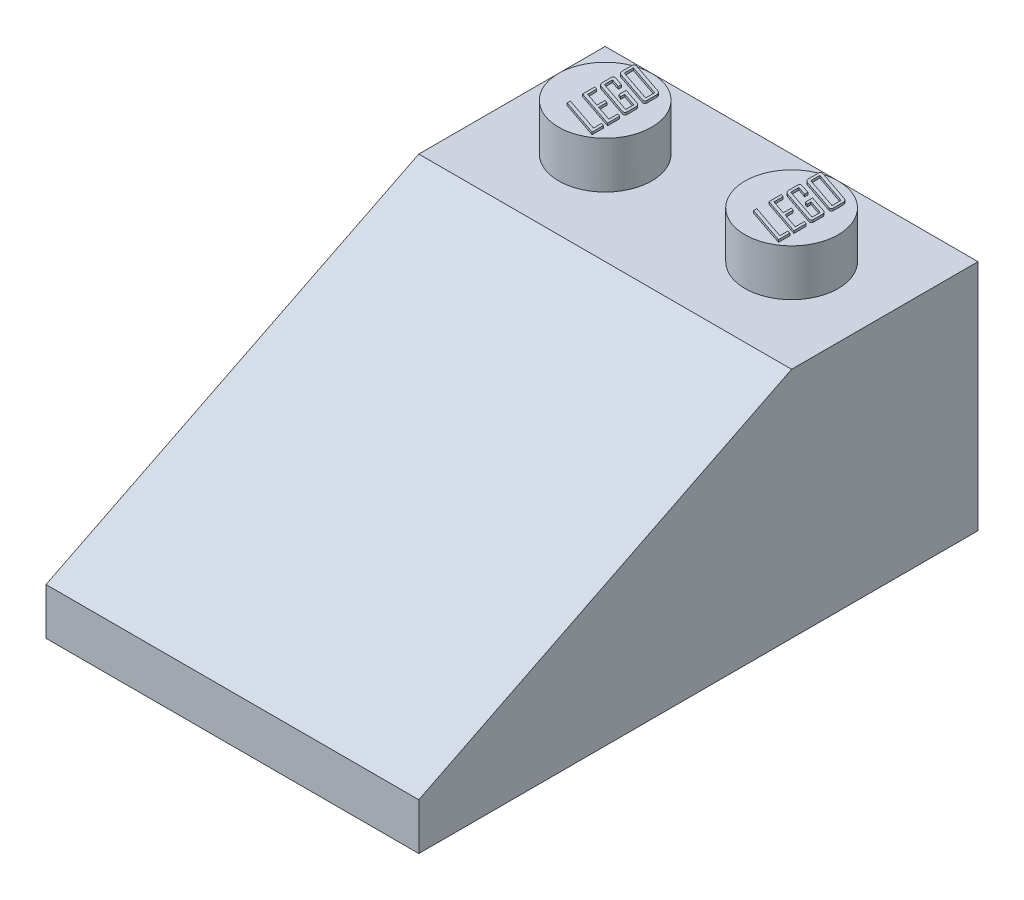
SolidWorks part; units mm, degrees
material "ABS"
ref_plane "Front Plane" through (0, 0, 0) normal (0, 0, 1) x (1, 0, 0)
ref_plane "Top Plane" through (0, 0, 0) normal (0, 1, 0) x (1, 0, 0)
ref_plane "Right Plane" through (0, 0, 0) normal (1, 0, 0) x (0, 0, -1)
sketch "Sketch1" plane through (0, 0, 0) normal (1, 0, 0) x (0, 0, -1)
  line L0 (-24, 0) -> (0, 0)
  line L1 (0, 0) -> (0, 10)
  line L2 (0, 10) -> (-8, 10)
  line L3 (-8, 10) -> (-24, 2)
  line L4 (-24, 2) -> (-24, 0)
  dimension "D1" = 24
  dimension "D2" = 10
  dimension "D3" = 8
  dimension "D4" = 2
extrude "Boss-Extrude1" add sketch "Sketch1" along normal blind 16
sketch "Sketch2" plane through (0, 10, 0) normal (0, 1, 0) x (1, 0, 0)
  line L0 (8, 0) -> (8, -8) construction
  line L1 (16, 0) -> (0, 0) construction
  line L2 (16, -8) -> (0, -8) construction
  line L3 (0, 0) -> (0, -8) construction
  circle A0 centre (4, -4) radius 2
  circle A1 centre (12, -4) radius 2
  dimension "D1" = 4
  dimension "D2" = 4
  dimension "D3" = 4
extrude "Boss-Extrude2" add sketch "Sketch2" along normal blind 2
shell "Shell1" thickness 1
sketch "Sketch3" plane through (0, 0, 0) normal (0, -1, 0) x (1, 0, 0)
  line L0 (8, 8) -> (8, 0) construction
  line L2 (16, 0) -> (0, 0) construction
  line L4 (16, 12) -> (0, 12) construction
  line L5 (16, 24) -> (16, 0) construction
  line L6 (0, 24) -> (0, 0) construction
  circle A0 centre (8, 8) radius 2.7
  circle A1 centre (8, 8) radius 1.7
  circle A2 centre (8, 16) radius 1.7
  circle A3 centre (8, 16) radius 2.7
  dimension "D2" = 5.4
  dimension "D3" = 3.4
  dimension "D1" = 8
extrude "Boss-Extrude3" add sketch "Sketch3" against normal up to next
sketch "Sketch4" plane through (0, 12, 0) normal (0, 1, 0) x (1, 0, 0)
  line L0 (4, -6) -> (4, -2) construction
  line L1 (4, -2) -> (5, -2) construction
  line L2 (5, -2) -> (5, -5.7) construction
  circle A2 centre (4, -4) radius 2 construction
  circle A3 centre (4, -4) radius 2 construction
  text T0 "<i>LEGO</i>" font "Agency FB" height in points 6
  dimension "D1" = 1
  dimension "D2" = 3.7
extrude "Boss-Extrude6" add sketch "Sketch4" along normal blind 0.1
sketch "Sketch5" plane through (0, 12, 0) normal (0, 1, 0) x (1, 0, 0)
  line L0 (12, -6) -> (12, -2) construction
  line L1 (12, -2) -> (13, -2) construction
  line L2 (13, -2) -> (13, -5.7) construction
  circle A0 centre (12, -4) radius 2 construction
  circle A1 centre (12, -4) radius 2 construction
  text T0 "<i>LEGO</i>" font "Agency FB" height in points 6
  dimension "D1" = 1
  dimension "D2" = 3.7
extrude "Boss-Extrude7" add sketch "Sketch5" along normal blind 0.1
